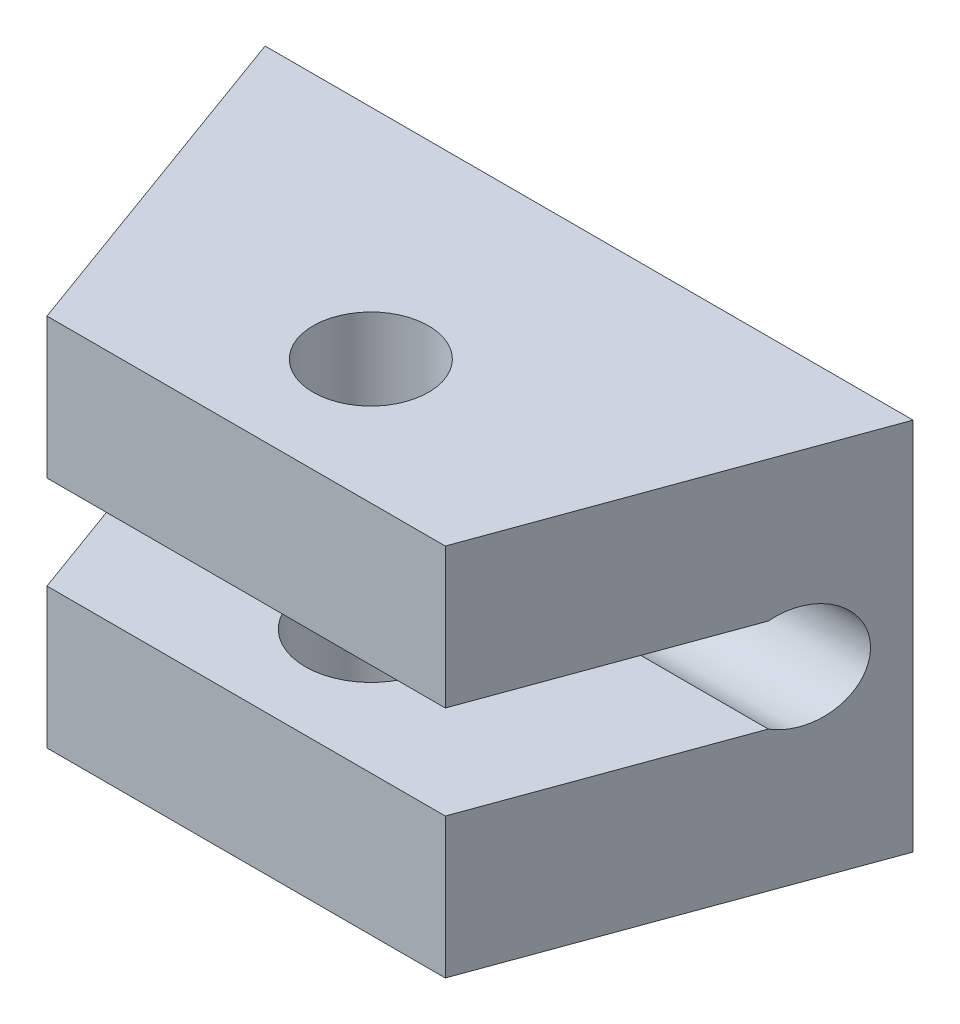
SolidWorks part; units mm, degrees
ref_plane "Front Plane" through (0, 0, 0) normal (0, 0, 1) x (1, 0, 0)
ref_plane "Top Plane" through (0, 0, 0) normal (0, 1, 0) x (1, 0, 0)
ref_plane "Right Plane" through (0, 0, 0) normal (1, 0, 0) x (0, 0, -1)
sketch "Sketch8" plane through (0, 0, 0) normal (0, 0, 1) x (1, 0, 0)
  line L0 (4.0623, 3) -> (-4.0623, 3) construction
  line L1 (5.1962, -3) -> (-5.1962, -3)
  line L2 (5.1962, -3) -> (5.1962, 3)
  line L3 (5.1962, 3) -> (-5.1962, 3)
  line L4 (-5.1962, -3) -> (-5.1962, 3)
  circle A0 centre (0, 0) radius 6 construction
extrude "Boss-Extrude3" add sketch "Sketch8" along normal blind 5.5
sketch "Sketch9" plane through (5.1962, 0, 0) normal (1, 0, 0) x (0, 0, -1)
  line L0 (-0.5, 0) -> (-1.335, 0) construction
  line L1 (0, -3) -> (0, 3) construction
  line L2 (-5.5, -3) -> (-5.5, 3) construction
  line L3 (-1.702, 0.75) -> (-5.5, 0.75)
  line L4 (-1.702, 0.75) -> (-1.702, -0.75) construction
  line L5 (-1.702, -0.75) -> (-5.5, -0.75)
  line L6 (-5.5, 0.75) -> (-5.5, -0.75)
  arc A0 (-1.702, -0.75) -> (-1.702, 0.75) centre (-1.335, 0) ccw
  dimension "D1" = 1.67
  dimension "D2" = 1.5
  dimension "D3" = 0.5
extrude "Cut-Extrude5" cut sketch "Sketch9" against normal through all
sketch "Sketch11" plane through (0, 3, 0) normal (0, 1, 0) x (1, 0, 0)
  line L0 (0, 0) -> (0, -3.5) construction
  line L1 (5.1962, -5.5) -> (-5.1962, -5.5) construction
  circle A0 centre (0, -3.5) radius 0.925
  dimension "D1" = 1.85
  dimension "D2" = 2
extrude "Cut-Extrude7" cut sketch "Sketch11" against normal up to next
sketch "Sketch12" plane through (0, -0.75, 0) normal (0, 1, 0) x (1, 0, 0)
  circle A0 centre (0, -3.5) radius 1.05
  dimension "D1" = 2.1
extrude "Cut-Extrude8" cut sketch "Sketch12" against normal up to next
sketch "Sketch10" plane through (0, -3, 0) normal (0, -1, 0) x (1, 0, 0)
  line L0 (5.1962, 0) -> (3.1943, 5.5)
  line L1 (-5.1962, 5.5) -> (5.1962, 5.5) construction
  line L2 (3.1943, 5.5) -> (5.1962, 5.5)
  line L3 (5.1962, 5.5) -> (5.1962, 0)
  line L4 (0, 0) -> (0, 5.5) construction
  line L5 (-5.1962, 5.5) -> (-5.1962, 0)
  line L6 (-3.1943, 5.5) -> (-5.1962, 5.5)
  line L7 (-5.1962, 0) -> (-3.1943, 5.5)
  dimension "D1" = 70
extrude "Cut-Extrude6" cut sketch "Sketch10" against normal through all
